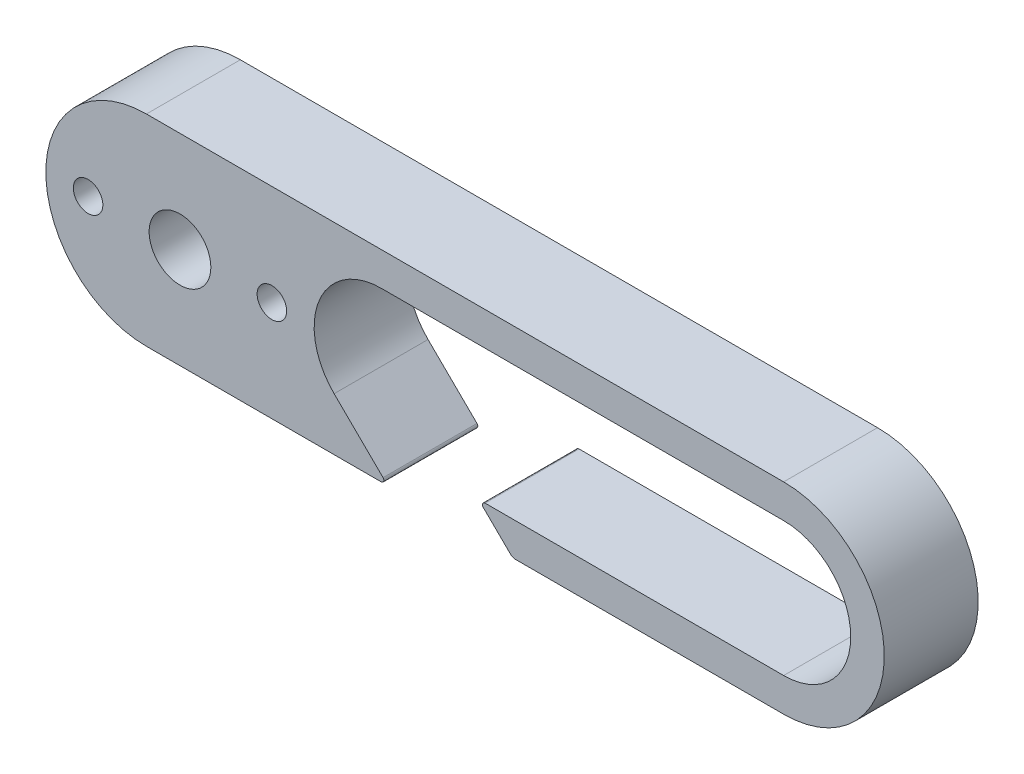
SolidWorks part; units mm, degrees
ref_plane "Front Plane" through (0, 0, 0) normal (0, 0, 1) x (1, 0, 0)
ref_plane "Top Plane" through (0, 0, 0) normal (0, 1, 0) x (1, 0, 0)
ref_plane "Right Plane" through (0, 0, 0) normal (1, 0, 0) x (0, 0, -1)
sketch "Sketch2" plane through (0, 0, 0) normal (0, 0, 1) x (1, 0, 0)
  line L0 (2.7704, 0) -> (54.3236, 0) construction
  line L1 (16.7704, 5) -> (46.7704, 5)
  line L2 (24.516, -5) -> (46.7704, -5)
  line L3 (-0.7296, 7.5) -> (46.7704, 7.5)
  line L4 (-0.7296, -7.5) -> (16.7704, -7.5)
  line L5 (-0.7296, 5) -> (46.7704, 5) construction
  line L6 (-0.7296, -5) -> (46.7704, -5) construction
  line L7 (11.7704, 0) -> (46.7704, 0) construction
  line L8 (13.2611, -3.5616) -> (16.9094, -7.1562)
  line L10 (26.4194, -7.3562) -> (24.3757, -5.3425)
  line L12 (26.7704, -7.5) -> (46.7704, -7.5)
  line L13 (-0.7296, -7.5) -> (46.7704, -7.5) construction
  line L15 (11.7704, 0) -> (-8.2296, 0) construction
  arc A1 (46.7704, -5) -> (46.7704, 5) centre (46.7704, 0) ccw
  arc A2 (46.7704, -7.5) -> (46.7704, 7.5) centre (46.7704, 0) ccw
  arc A3 (-0.7296, 7.5) -> (-0.7296, -7.5) centre (-0.7296, 0) ccw
  circle A4 centre (2.7704, 0) radius 2.5
  arc A6 (16.7704, 5) -> (13.2611, -3.5616) centre (16.7704, 0) ccw
  arc A7 (-0.7296, 5) -> (-0.7296, -5) centre (-0.7296, 0) ccw construction
  arc A8 (24.3757, -5.3425) -> (24.516, -5) centre (24.516, -5.2) cw
  arc A9 (26.7704, -7.5) -> (26.4194, -7.3562) centre (26.7704, -7) cw
  arc A10 (16.7704, -7.5) -> (16.9094, -7.1562) centre (16.7704, -7.3) ccw
  circle A11 centre (2.7704, 0) radius 2.2653 construction
  arc A12 (2.6037, 2.3451) -> (2.7704, 2.2653) centre (2.7704, 2.479) ccw
  arc A13 (2.6037, 2.3451) -> (2.2384, 2.2901) centre (2.4371, 2.2113) ccw
  arc A14 (2.1027, 2.1646) -> (2.2384, 2.2901) centre (2.0397, 2.3689) ccw
  arc A15 (2.7704, 2.2653) -> (2.937, 2.3451) centre (2.7704, 2.479) ccw
  arc A16 (3.3024, 2.2901) -> (2.937, 2.3451) centre (3.1037, 2.2113) ccw
  arc A17 (3.3024, 2.2901) -> (3.4381, 2.1646) centre (3.5011, 2.3689) ccw
  arc A18 (3.4381, 2.1646) -> (3.6209, 2.1918) centre (3.5011, 2.3689) ccw
  arc A19 (3.9537, 2.0315) -> (3.6209, 2.1918) centre (3.7406, 2.0148) ccw
  arc A20 (3.9537, 2.0315) -> (4.0464, 1.8716) centre (4.1669, 2.0483) ccw
  arc A21 (4.0464, 1.8716) -> (4.2291, 1.8438) centre (4.1669, 2.0483) ccw
  arc A22 (4.5, 1.5925) -> (4.2291, 1.8438) centre (4.2914, 1.6393) ccw
  arc A23 (4.5, 1.5925) -> (4.5414, 1.4124) centre (4.7086, 1.5456) ccw
  arc A24 (4.5414, 1.4124) -> (4.7078, 1.3319) centre (4.7086, 1.5456) ccw
  arc A25 (4.8925, 1.0119) -> (4.7078, 1.3319) centre (4.707, 1.1181) ccw
  arc A26 (4.8925, 1.0119) -> (4.879, 0.8276) centre (5.078, 0.9057) ccw
  arc A27 (4.879, 0.8276) -> (5.0143, 0.7016) centre (5.078, 0.9057) ccw
  arc A28 (5.0965, 0.3414) -> (5.0143, 0.7016) centre (4.9505, 0.4976) ccw
  arc A29 (5.0965, 0.3414) -> (5.0293, 0.1693) centre (5.2425, 0.1853) ccw
  arc A30 (5.0293, 0.1693) -> (5.1214, 0.0091) centre (5.2425, 0.1853) ccw
  arc A31 (5.0938, -0.3594) -> (5.1214, 0.0091) centre (5.0004, -0.1671) ccw
  arc A32 (5.0938, -0.3594) -> (4.9788, -0.5041) centre (5.1872, -0.5516) ccw
  arc A33 (4.9788, -0.5041) -> (5.0196, -0.6843) centre (5.1872, -0.5516) ccw
  arc A34 (4.8846, -1.0283) -> (5.0196, -0.6843) centre (4.852, -0.817) ccw
  arc A35 (4.8846, -1.0283) -> (4.7321, -1.1326) centre (4.9173, -1.2395) ccw
  arc A36 (4.7321, -1.1326) -> (4.718, -1.3169) centre (4.9173, -1.2395) ccw
  arc A37 (4.4876, -1.6058) -> (4.718, -1.3169) centre (4.5187, -1.3943) ccw
  arc A38 (4.4876, -1.6058) -> (4.3111, -1.6606) centre (4.4565, -1.8173) ccw
  arc A39 (4.3111, -1.6606) -> (4.2433, -1.8325) centre (4.4565, -1.8173) ccw
  arc A40 (3.938, -2.0406) -> (4.2433, -1.8325) centre (4.0301, -1.8477) ccw
  arc A41 (3.938, -2.0406) -> (3.7532, -2.0409) centre (3.846, -2.2335) ccw
  arc A42 (3.7532, -2.0409) -> (3.6377, -2.1852) centre (3.846, -2.2335) ccw
  arc A43 (3.2847, -2.2941) -> (3.6377, -2.1852) centre (3.4295, -2.1369) ccw
  arc A44 (3.2847, -2.2941) -> (3.108, -2.24) centre (3.1398, -2.4513) ccw
  arc A45 (3.108, -2.24) -> (2.9551, -2.3438) centre (3.1398, -2.4513) ccw
  arc A46 (2.5856, -2.3438) -> (2.9551, -2.3438) centre (2.7704, -2.2362) ccw
  arc A47 (2.5856, -2.3438) -> (2.4328, -2.24) centre (2.4009, -2.4513) ccw
  arc A48 (2.4328, -2.24) -> (2.2561, -2.2941) centre (2.4009, -2.4513) ccw
  arc A49 (1.903, -2.1852) -> (2.2561, -2.2941) centre (2.1112, -2.1369) ccw
  arc A50 (1.903, -2.1852) -> (1.7875, -2.0409) centre (1.6948, -2.2335) ccw
  arc A51 (1.7875, -2.0409) -> (1.6027, -2.0406) centre (1.6948, -2.2335) ccw
  arc A52 (1.2974, -1.8325) -> (1.6027, -2.0406) centre (1.5107, -1.8477) ccw
  arc A53 (1.2974, -1.8325) -> (1.2296, -1.6606) centre (1.0842, -1.8173) ccw
  arc A54 (1.2296, -1.6606) -> (1.0531, -1.6058) centre (1.0842, -1.8173) ccw
  arc A55 (0.8227, -1.3169) -> (1.0531, -1.6058) centre (1.022, -1.3943) ccw
  arc A56 (0.8227, -1.3169) -> (0.8086, -1.1326) centre (0.6235, -1.2395) ccw
  arc A57 (0.8086, -1.1326) -> (0.6561, -1.0283) centre (0.6235, -1.2395) ccw
  arc A58 (0.5211, -0.6843) -> (0.6561, -1.0283) centre (0.6887, -0.817) ccw
  arc A59 (0.5211, -0.6843) -> (0.5619, -0.5041) centre (0.3535, -0.5516) ccw
  arc A60 (0.5619, -0.5041) -> (0.4469, -0.3594) centre (0.3535, -0.5516) ccw
  arc A61 (0.4193, 0.0091) -> (0.4469, -0.3594) centre (0.5404, -0.1671) ccw
  arc A62 (0.4193, 0.0091) -> (0.5114, 0.1693) centre (0.2983, 0.1853) ccw
  arc A63 (0.5114, 0.1693) -> (0.4442, 0.3414) centre (0.2983, 0.1853) ccw
  arc A64 (0.5265, 0.7016) -> (0.4442, 0.3414) centre (0.5902, 0.4976) ccw
  arc A65 (0.5265, 0.7016) -> (0.6617, 0.8276) centre (0.4627, 0.9057) ccw
  arc A66 (0.6617, 0.8276) -> (0.6482, 1.0119) centre (0.4627, 0.9057) ccw
  arc A67 (0.833, 1.3319) -> (0.6482, 1.0119) centre (0.8337, 1.1181) ccw
  arc A68 (0.833, 1.3319) -> (0.9993, 1.4124) centre (0.8322, 1.5456) ccw
  arc A69 (0.9993, 1.4124) -> (1.0408, 1.5925) centre (0.8322, 1.5456) ccw
  arc A70 (1.3116, 1.8438) -> (1.0408, 1.5925) centre (1.2493, 1.6393) ccw
  arc A71 (1.3116, 1.8438) -> (1.4943, 1.8716) centre (1.3739, 2.0483) ccw
  arc A72 (1.4943, 1.8716) -> (1.587, 2.0315) centre (1.3739, 2.0483) ccw
  arc A73 (1.9199, 2.1918) -> (1.587, 2.0315) centre (1.8001, 2.0148) ccw
  arc A74 (1.9199, 2.1918) -> (2.1027, 2.1646) centre (2.0397, 2.3689) ccw
  circle A75 centre (1.7704, 0) radius 1.05
  circle A76 centre (1.7704, 0) radius 2.3
  circle A77 centre (6.6204, 0) radius 1.1
  circle A78 centre (8.6204, 0) radius 1.1
  circle A79 centre (10.6204, 0) radius 1.1
  circle A80 centre (-3.0796, 0) radius 1.1
  circle A81 centre (-5.0796, 0) radius 1.1
  circle A82 centre (-7.0796, 0) radius 1.1
  point P3 (25, 0)
  point P32 (2.7704, 0)
  point P34 (2.7704, 0)
  point P159 (2.7704, 0)
  point P176 (1.7704, 0)
  dimension "D2" = 30
  dimension "D3" = 47.5
  dimension "D5" = 5
  dimension "D6" = 5
  dimension "D7" = 5
  dimension "D8" = 0.2
  dimension "D9" = 0.5
  dimension "D10" = 0.2
  dimension "D20" = 2.2
  dimension "D1" = 2.5
  dimension "D4" = 3.5
  dimension "D11" = 10
  dimension "D12" = 2.2362
  dimension "D13" = 2
  dimension "D14" = 2
  dimension "D15" = 2
  dimension "D16" = 2
  dimension "D17" = 4.85
  dimension "D18" = 4.85
  dimension "D19" = 20
extrude "Boss-Extrude1" add sketch "Sketch2" along normal blind 7 contours A82 A3 L4 A10 L8 A6 A79 L1 A1 L2 A8 L10 A9 L12 A2 L3 A81 A80 A78 A77 A4 A76 | A6 A79 | A77 A28 A27 A26 A25 A24 A23 A22 A21 A20 A19 A18 A17 A16 A15 A12 A13 A14 A74 A73 A76 A52 A51 A50 A49 A48 A47 A46 A45 A44 A43 A42 A41 A40 A39 A38 A37 A36 A35 A34 A33 A32 | A76 A73 A74 A14 A13 A12 A15 A16 A17 A18 A19 A20 A21 A22 A23 A24 A25 A26 A27 A28 A29 A30 A31 A32 A33 A34 A35 A36 A37 A38 A39 A40 A41 A42 A43 A44 A45 A46 A47 A48 A49 A50 A4 | A78 A77 | A81 A80 | A81 A82 | A75
